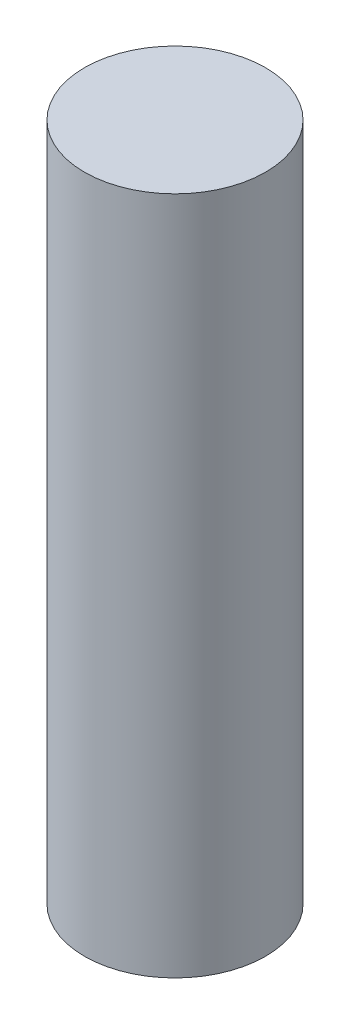
SolidWorks part; units mm, degrees
ref_plane "Plan de face" through (0, 0, 0) normal (0, 0, 1) x (1, 0, 0)
ref_plane "Plan de dessus" through (0, 0, 0) normal (0, 1, 0) x (1, 0, 0)
ref_plane "Plan de droite" through (0, 0, 0) normal (1, 0, 0) x (0, 0, -1)
sketch "Esquisse1" plane through (0, 0, 0) normal (0, 1, 0) x (1, 0, 0)
  circle A0 centre (0, 0) radius 2
extrude "Boss.-Extru.1" add sketch "Esquisse1" along normal blind 15
